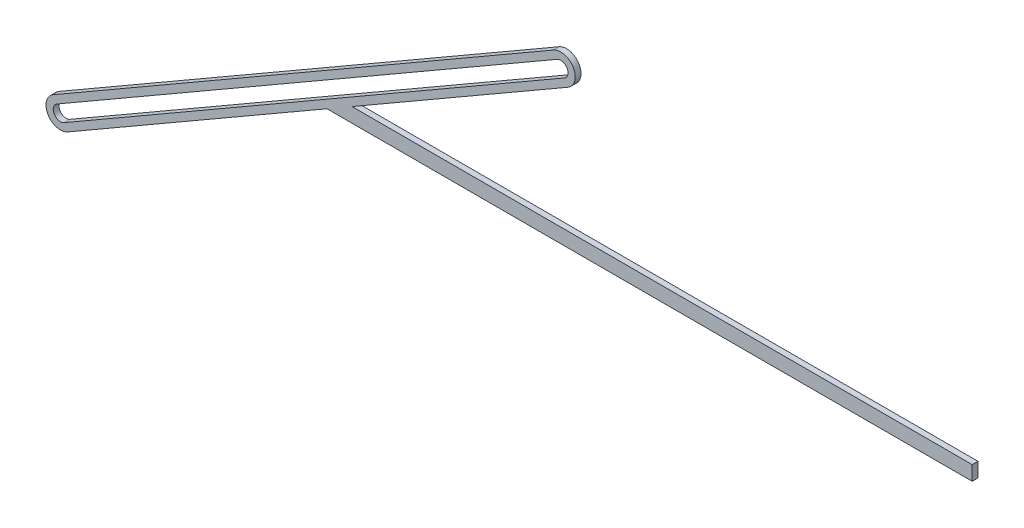
SolidWorks part; units mm, degrees
ref_plane "前视基准面" through (0, 0, 0) normal (0, 0, 1) x (1, 0, 0)
ref_plane "上视基准面" through (0, 0, 0) normal (0, 1, 0) x (1, 0, 0)
ref_plane "右视基准面" through (0, 0, 0) normal (1, 0, 0) x (0, 0, -1)
sketch "草图1" plane through (0, 0, 0) normal (0, 0, 1) x (1, 0, 0)
  line L0 (-196.6718, 5) -> (-47.127, 91.3397)
  line L1 (-401.0372, -95.6699) -> (-54.627, 104.3301)
  line L2 (-393.5372, -108.6603) -> (-213.9923, -5)
  line L3 (-403.5372, -91.3397) -> (-57.127, 108.6603)
  line L4 (-396.0372, -104.3301) -> (-49.627, 95.6699)
  line L5 (-393.5372, -108.6603) -> (-47.127, 91.3397) construction
  line L7 (84.0395, 5) -> (162.4328, 5)
  line L9 (162.4328, -5) -> (84.0395, -5)
  line L10 (-213.9923, -5) -> (84.0395, -5)
  line L11 (162.4328, 5) -> (232.7166, 5)
  line L12 (-196.6718, 5) -> (84.0395, 5)
  line L13 (232.7166, 5) -> (232.7166, -5)
  line L14 (232.7166, -5) -> (162.4328, -5)
  arc A0 (-47.127, 91.3397) -> (-57.127, 108.6603) centre (-52.127, 100) ccw
  arc A1 (-403.5372, -91.3397) -> (-393.5372, -108.6603) centre (-398.5372, -100) ccw
  arc A2 (-49.627, 95.6699) -> (-54.627, 104.3301) centre (-52.127, 100) ccw
  arc A3 (-401.0372, -95.6699) -> (-396.0372, -104.3301) centre (-398.5372, -100) ccw
  point P5 (-225.3321, 0)
  dimension "D1" = 5
  dimension "D2" = 200
  dimension "D3" = 200
extrude "凸台-拉伸1" add sketch "草图1" along normal blind 4
